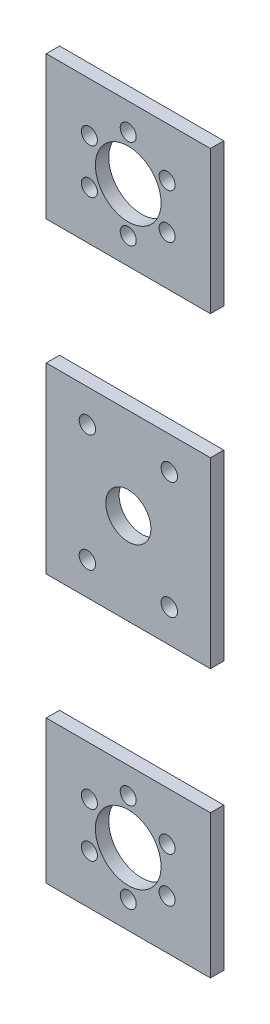
SolidWorks part; units mm, degrees
material "Alloy Steel"
ref_plane "Front Plane" through (0, 0, 0) normal (0, 0, 1) x (1, 0, 0)
ref_plane "Top Plane" through (0, 0, 0) normal (0, 1, 0) x (1, 0, 0)
ref_plane "Right Plane" through (0, 0, 0) normal (1, 0, 0) x (0, 0, -1)
sketch "Sketch2" plane through (0, 0, 0) normal (0, 0, 1) x (1, 0, 0)
  line L1 (-40, 175) -> (40, 175)
  line L2 (-40, 175) -> (-40, -175)
  line L3 (-40, -175) -> (40, -175)
  line L4 (40, 175) -> (40, -175)
  line L5 (-40, 175) -> (40, -175) construction
  line L6 (-40, -175) -> (40, 175) construction
  point P0 (0, 0)
  dimension "D1" = 350
  dimension "D2" = 80
extrude "Boss-Extrude1" add sketch "Sketch2" along normal blind 6.5
sketch "Sketch3" plane through (0, 0, 6.5) normal (0, 0, 1) x (1, 0, 0)
  line L0 (-0.0594, 175) -> (0.0594, -175) construction
  line L1 (0, 0) -> (72.0486, 0) construction
  line L2 (40, 175) -> (-40, 175) construction
  line L3 (25.2003, 28.5121) -> (14.7003, 28.5121) construction
  line L4 (19.9503, 28.5121) -> (-19.9503, -28.5121) construction
  circle A0 centre (0, 0) radius 11
  circle A1 centre (-0.0475, 140) radius 16
  circle A2 centre (-0.0475, -140) radius 16
  circle A4 centre (-0.0475, 118.13) radius 3.9
  circle A5 centre (-18.9875, 129.065) radius 3.9
  circle A6 centre (-18.9875, 150.935) radius 3.9
  circle A7 centre (-0.0475, 161.87) radius 3.9
  circle A8 centre (18.8924, 150.935) radius 3.9
  circle A9 centre (18.8924, 129.065) radius 3.9
  circle A10 centre (18.8924, -129.065) radius 3.9
  circle A11 centre (18.8924, -150.935) radius 3.9
  circle A12 centre (-0.0475, -161.87) radius 3.9
  circle A13 centre (-18.9875, -150.935) radius 3.9
  circle A14 centre (-18.9875, -129.065) radius 3.9
  circle A15 centre (-0.0475, -118.13) radius 3.9
  circle A17 centre (19.9503, 28.5121) radius 4
  circle A18 centre (-19.9503, 28.4985) radius 4
  circle A19 centre (19.9503, -28.5256) radius 4
  circle A20 centre (-19.9503, -28.5121) radius 4
  point P33 (-0.0475, 140)
  dimension "D2" = 22
  dimension "D3" = 32
  dimension "D1" = 35
extrude "Cut-Extrude1" cut sketch "Sketch3" against normal through all
ref_plane "Plane1" through (0, 0, 6.5) normal (0, 0, 1) x (1, 0, 0)
sketch "Sketch4" plane through (0, 0, 6.5) normal (0, 0, 1) x (1, 0, 0)
  line L0 (-85.414, 0) -> (135.0658, 0) construction
  line L1 (-41.1706, 174.7141) -> (41.0755, 174.7141) construction
  line L2 (-41.1706, 174.7141) -> (-41.1706, 105.2859) construction
  line L3 (-41.1706, 105.2859) -> (41.0755, 105.2859) construction
  line L4 (41.0755, 174.7141) -> (41.0755, 105.2859) construction
  line L5 (-41.1706, 174.7141) -> (41.0755, 105.2859) construction
  line L6 (-41.1706, 105.2859) -> (41.0755, 174.7141) construction
  line L7 (-41.0755, -44.5142) -> (41.0755, -44.5142)
  line L8 (-41.0755, -44.5142) -> (-41.0755, 44.5142)
  line L9 (-41.0755, 44.5142) -> (41.0755, 44.5142)
  line L10 (41.0755, -44.5142) -> (41.0755, 44.5142)
  line L11 (-41.0755, -44.5142) -> (41.0755, 44.5142) construction
  line L12 (-41.0755, 44.5142) -> (41.0755, -44.5142) construction
  line L13 (-68.8644, -105.2859) -> (68.8169, -44.5142) construction
  line L14 (-68.8644, 44.5142) -> (68.8169, 44.5142)
  line L15 (-68.8644, 44.5142) -> (-68.8644, 105.2859)
  line L16 (-68.8644, 105.2859) -> (68.8169, 105.2859)
  line L17 (68.8169, 44.5142) -> (68.8169, 105.2859)
  line L18 (-68.8644, 44.5142) -> (68.8169, 105.2859) construction
  line L19 (-68.8644, 105.2859) -> (68.8169, 44.5142) construction
  line L20 (-68.8644, -44.5142) -> (68.8169, -105.2859) construction
  line L21 (-41.1706, -105.2859) -> (41.0755, -105.2859) construction
  line L22 (68.8169, -44.5142) -> (68.8169, -105.2859)
  line L23 (-68.8644, -105.2859) -> (68.8169, -105.2859)
  line L24 (-68.8644, -44.5142) -> (-68.8644, -105.2859)
  line L25 (-68.8644, -44.5142) -> (68.8169, -44.5142)
  line L26 (-41.0755, -44.5142) -> (41.0755, -44.5142)
  point P0 (-0.0475, 140)
  point P6 (0, 0)
  point P14 (-0.0238, 74.9001)
  point P26 (-0.0238, -74.9001)
extrude "Cut-Extrude2" cut sketch "Sketch4" against normal through all contours L14 L17 L16 L15 L9 | L25 L24 L23 L22 L7
